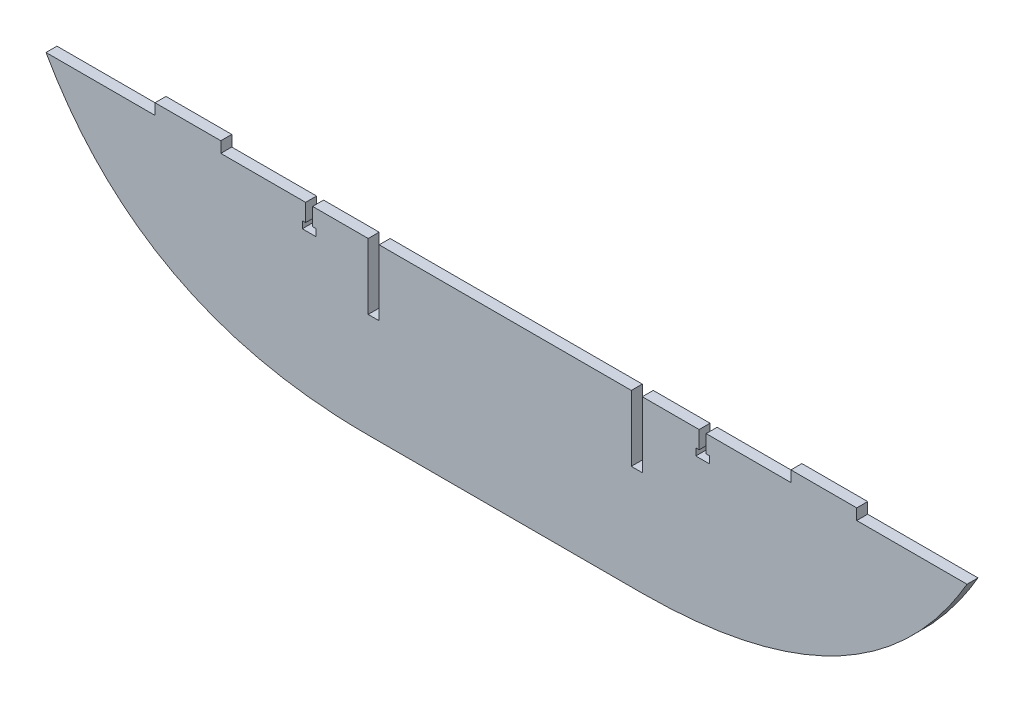
SolidWorks part; units mm, degrees
ref_plane "Front Plane" through (0, 0, 0) normal (0, 0, 1) x (1, 0, 0)
ref_plane "Top Plane" through (0, 0, 0) normal (0, 1, 0) x (1, 0, 0)
ref_plane "Right Plane" through (0, 0, 0) normal (1, 0, 0) x (0, 0, -1)
sketch "Sketch1" plane through (0, 0, 0) normal (0, 0, 1) x (1, 0, 0)
  line L0 (72.6619, 406.4766) -> (72.6619, 347.9782) construction
  line L1 (-193.675, 406.4) -> (-130.5381, 406.4)
  line L2 (-130.5381, 406.4) -> (-130.5381, 412.75)
  line L3 (-6.35, 307.7927) -> (152.4, 307.7927)
  line L4 (-193.675, 412.75) -> (339.725, 412.75) construction
  line L5 (-130.5381, 412.75) -> (-92.4381, 412.75)
  line L6 (-92.4381, 412.75) -> (-92.4381, 406.4)
  line L7 (-92.4381, 406.4) -> (-43.3169, 406.4)
  line L8 (237.7619, 412.75) -> (237.7619, 406.4)
  line L9 (275.8619, 406.4) -> (275.8619, 412.75)
  line L10 (275.8619, 412.75) -> (237.7619, 412.75)
  line L11 (275.8619, 406.4) -> (339.7514, 406.4)
  line L12 (-43.3169, 406.4) -> (-43.3169, 396.24)
  line L13 (-6.35, 368.3) -> (-0.7262, 368.3)
  line L14 (-43.3169, 396.24) -> (-45.2219, 396.24)
  line L15 (0, 406.4) -> (145.3238, 406.4)
  line L16 (145.3238, 406.4) -> (145.3238, 368.3)
  line L17 (145.3238, 368.3) -> (151.6738, 368.3)
  line L18 (151.6738, 368.3) -> (151.6738, 406.4)
  line L19 (152.4, 406.4) -> (184.5767, 406.4)
  line L20 (151.6738, 406.4) -> (152.4, 406.4)
  line L21 (-7.0762, 406.4) -> (-7.0762, 368.3)
  line L22 (-7.0762, 368.3) -> (-6.35, 368.3)
  line L23 (-0.7262, 406.4) -> (0, 406.4)
  line L24 (-0.7262, 406.4) -> (-7.0762, 406.4) construction
  line L25 (-0.7262, 406.4) -> (-0.7262, 368.3)
  line L26 (-45.2219, 396.24) -> (-45.2219, 392.176)
  line L27 (-45.2219, 392.176) -> (-37.3479, 392.176)
  line L28 (-41.2849, 392.176) -> (-41.2849, 406.4) construction
  line L29 (-37.3479, 396.24) -> (-37.3479, 392.176)
  line L30 (-39.2529, 396.24) -> (-37.3479, 396.24)
  line L31 (-39.2529, 406.4) -> (-39.2529, 396.24)
  line L32 (-39.2529, 406.4) -> (-7.0762, 406.4)
  line L33 (186.6087, 392.176) -> (186.6087, 406.4) construction
  line L34 (184.5767, 406.4) -> (184.5767, 396.24)
  line L35 (184.5767, 396.24) -> (182.6717, 396.24)
  line L36 (182.6717, 396.24) -> (182.6717, 392.176)
  line L37 (190.5457, 392.176) -> (182.6717, 392.176)
  line L38 (190.5457, 396.24) -> (190.5457, 392.176)
  line L39 (188.6407, 396.24) -> (190.5457, 396.24)
  line L40 (188.6407, 406.4) -> (188.6407, 396.24)
  line L41 (188.6407, 406.4) -> (237.7619, 406.4)
  spline S0 degree 2 poles (-193.675, 406.4) (-138.0103, 307.4403) (-6.35, 307.7927) knots 0 0 0 1 1 1
  spline S1 degree 2 poles (152.4, 307.7927) (282.8477, 308.4739) (339.7514, 406.4) knots 0 0 0 1 1 1
  dimension "D1" = 38.1
  dimension "D2" = 165.1
  dimension "D3" = 238.76
  dimension "D4" = 38.1
  dimension "D5" = 238.76
  dimension "D6" = 38.1
  dimension "D7" = 4.064
  dimension "D8" = 3.937
  dimension "D9" = 14.224
  dimension "D10" = 4.064
extrude "Boss-Extrude13" add sketch "Sketch1" along normal blind 6.35
